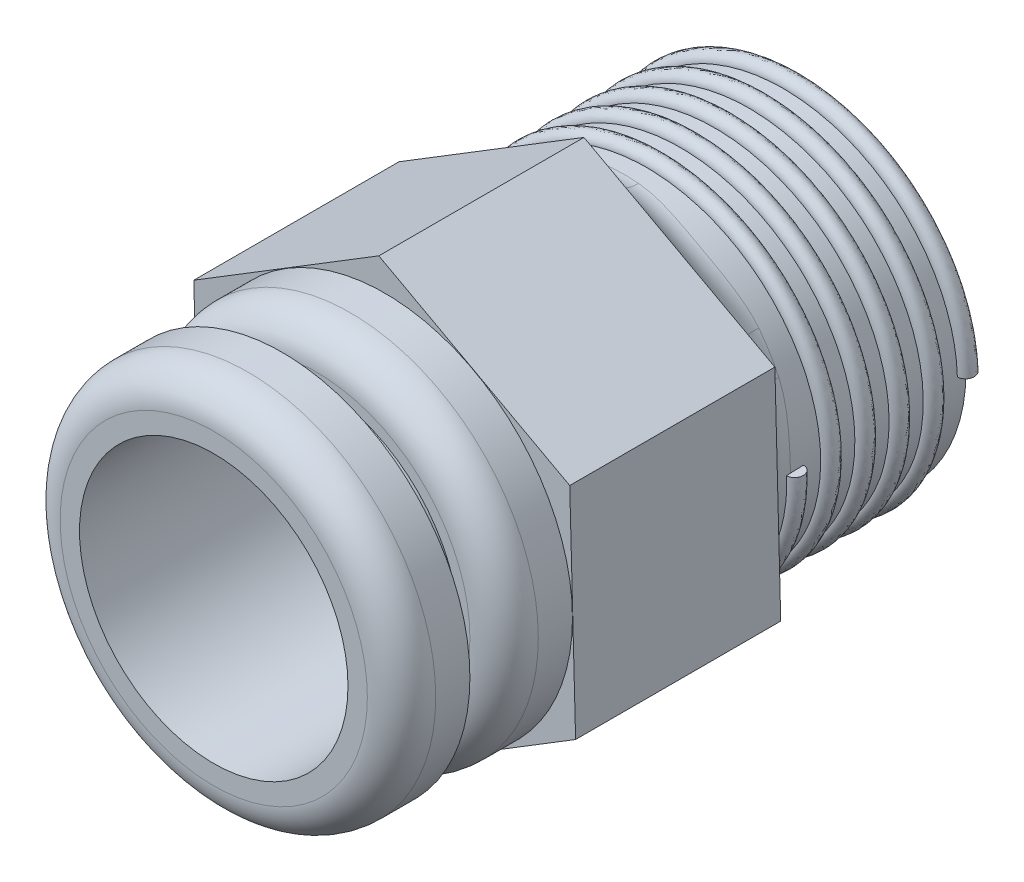
SolidWorks part; units mm, degrees
ref_plane "Front Plane" through (0, 0, 0) normal (0, 0, 1) x (1, 0, 0)
ref_plane "Top Plane" through (0, 0, 0) normal (0, 1, 0) x (1, 0, 0)
ref_plane "Right Plane" through (0, 0, 0) normal (1, 0, 0) x (0, 0, -1)
sketch "Sketch1" plane through (0, 0, 0) normal (0, 0, 1) x (1, 0, 0)
  circle A0 centre (0, 0) radius 5
  dimension "D1" = 10
extrude "Boss-Extrude1" add sketch "Sketch1" along normal blind 6
sketch "Sketch2" plane through (0, 0, 6) normal (0, 0, 1) x (1, 0, 0)
  line L1 (5.5839, -3.0255) -> (5.4121, 3.323)
  line L2 (5.4121, 3.323) -> (-0.1717, 6.3485)
  line L3 (-0.1717, 6.3485) -> (-5.5839, 3.0255)
  line L4 (-5.5839, 3.0255) -> (-5.4121, -3.323)
  line L5 (-5.4121, -3.323) -> (0.1717, -6.3485)
  line L6 (0.1717, -6.3485) -> (5.5839, -3.0255)
  circle A0 centre (0, 0) radius 5.5 construction
  dimension "D1" = 11
extrude "Boss-Extrude2" add sketch "Sketch2" along normal blind 6
fillet "Fillet1" radius 1 1 edges at (5, 0, 6)
sketch "Sketch3" plane through (0, 0, 12) normal (0, 0, 1) x (1, 0, 0)
  circle A0 centre (0, 0) radius 5.4924
extrude "Boss-Extrude3" add sketch "Sketch3" along normal blind 2
fillet "Fillet2" radius 1 1 edges at (5.4924, 0, 14)
sketch "Sketch4" plane through (0, 0, 14) normal (0, 0, 1) x (1, 0, 0)
  circle A0 centre (0, 0) radius 4.1845
  circle A1 centre (0, 0) radius 3.9266
extrude "Boss-Extrude4" add sketch "Sketch4" along normal blind 1
sketch "Sketch5" plane through (0, 0, 15) normal (0, 0, 1) x (1, 0, 0)
  circle A0 centre (0, 0) radius 3.9266
  circle A1 centre (0, 0) radius 5.4924
extrude "Boss-Extrude5" add sketch "Sketch5" along normal blind 2
fillet "Fillet3" radius 1 1 edges at (5.4924, 0, 17)
sketch "Sketch6" plane through (0, 0, 14) normal (0, 0, 1) x (1, 0, 0)
  circle A0 centre (0, 0) radius 3.9266
extrude "Cut-Extrude1" cut sketch "Sketch6" against normal blind 32
sketch "Sketch7" plane through (0, 0, 0) normal (1, 0, 0) x (0, 0, -1)
  line L0 (0, -5) -> (0, 5) construction
  point P0 (0, 4.4456)
sketch "Sketch8" plane through (0, 0, 0) normal (0, 1, 0) x (1, 0, 0)
  line L1 (-5, 0) -> (-5, -5.1327) construction
  circle A0 centre (-5, 0) radius 0.25
  point P0 (-5, 0)
  point P2 (-5, 0)
  point P5 (0, 0)
  point P6 (0, 0)
  point P7 (0, 0)
  dimension "D1" = 0.5
sketch "Sketch9" plane through (0, 0, 0) normal (1, 0, 0) x (0, 0, -1)
  line L0 (0, 0) -> (-17.291, 0) construction
ref_plane "Plane1" through (0, 0, 0) normal (0, -1, 0) x (-1, 0, 0)
ref_plane "Plane2" through (0, 0, 0) normal (-1, 0, 0) x (0, 0, 1)
sketch "Sketch10" plane through (0, 0, 0) normal (-1, 0, 0) x (0, 0, 1)
  circle A0 centre (0, 4.4456) radius 0.25
  dimension "D1" = 0.5
sketch "Sketch11" plane through (0, 0, 0) normal (0, 0, -1) x (-1, 0, 0)
  circle A2 centre (0, 0) radius 5
curve "Helix/Spiral1" pitch 1 height 5 turns 5
ref_plane "Plane3" through (5, 0, 0) normal (0, 0.9995, 0.0318) x (1, 0, 0)
sketch "Sketch13" plane through (5, 0, 0) normal (0, 0.9995, 0.0318) x (1, 0, 0)
  circle A0 centre (0, 0) radius 0.25
  dimension "D1" = 0.5
sweep "Sweep2" add profiles "Sketch13" path "Helix/Spiral1"
